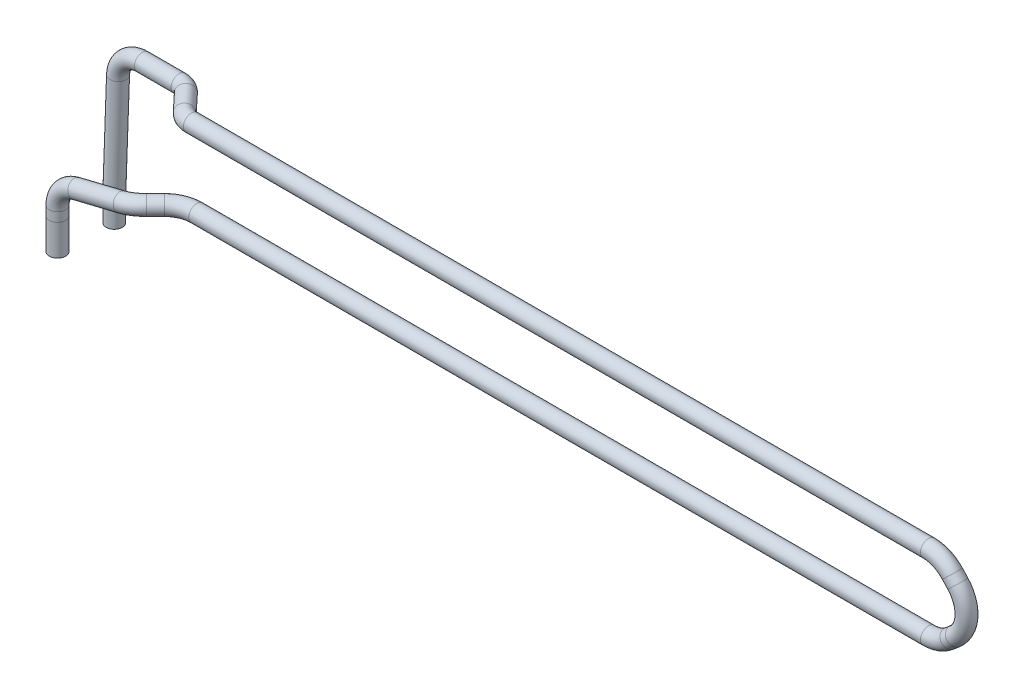
SolidWorks part; units mm, degrees
ref_plane "Front Plane" through (0, 0, 0) normal (0, 0, 1) x (1, 0, 0)
ref_plane "Top Plane" through (0, 0, 0) normal (0, 1, 0) x (1, 0, 0)
ref_plane "Right Plane" through (0, 0, 0) normal (1, 0, 0) x (0, 0, -1)
sketch3d "3DSketch1"
  line L0 (-61.7174, -11.5646, -3.1615) -> (-61.7174, -11.5646, 6.5143) construction
  line L1 (-62.0906, -9.4554, 3.4467) -> (-62.0906, -10.5909, 3.4467)
  line L3 (-52.0259, -4.8693, 2.533) -> (-50.944, -4.8693, 1.4511)
  line L4 (-48.1156, -4.8693, 0.2796) -> (41.8919, -4.8693, 0.2796)
  line L5 (44.494, -3.9073, 0.2796) -> (45.1703, -3.328, 0.2796)
  line L6 (45.4991, 2.432, 0.2796) -> (44.8228, 3.1602, 0.2796)
  line L7 (41.8919, 4.4381, 0.2796) -> (-48.7759, 4.4381, 0.2796)
  line L8 (-50.2366, 4.4381, -0.3542) -> (-52.2696, 4.4381, -2.5277)
  line L9 (-53.7302, 4.4381, -3.1615) -> (-58.2522, 4.4381, -3.1615)
  line L10 (-61.2503, 1.5449, -3.1615) -> (-61.7174, -11.5646, -3.1615)
  line L11 (-54.1951, -5.1752, 3.4467) -> (-59.8006, -6.5406, 3.4467)
  line L12 (-62.0906, -10.5909, 3.4467) -> (-62.0906, -14.4017, 3.4467)
  line L13 (-61.7174, -11.5646, -3.1615) -> (-61.7174, -14.4495, -3.1615)
  line L14 (41.8919, 4.4381, 0.2796) -> (41.8919, -4.8693, 0.2796) construction
  arc A0 (-61.2503, 1.5449, -3.1615) -> (-58.2522, 4.4381, -3.1615) centre (-58.2522, 1.4381, -3.1615) ccw
  arc A1 (-48.7759, 4.4381, 0.2796) -> (-50.2366, 4.4381, -0.3542) centre (-48.7759, 4.4381, -1.7204) ccw
  arc A2 (-53.7302, 4.4381, -3.1615) -> (-52.2696, 4.4381, -2.5277) centre (-53.7302, 4.4381, -1.1615) ccw
  arc A3 (-52.0259, -4.8693, 2.533) -> (-54.1951, -5.1752, 3.4467) centre (-54.0316, -5.8464, 0.5274) ccw
  arc A4 (-62.0906, -9.4554, 3.4467) -> (-59.8006, -6.5406, 3.4467) centre (-59.0906, -9.4554, 3.4467) ccw
  arc A5 (41.8919, 4.4381, 0.2796) -> (44.8228, 3.1602, 0.2796) centre (41.8919, 0.4381, 0.2796) ccw
  arc A6 (45.1703, -3.328, 0.2796) -> (45.4991, 2.432, 0.2796) centre (42.5682, -0.2901, 0.2796) ccw
  arc A7 (41.8919, -4.8693, 0.2796) -> (44.494, -3.9073, 0.2796) centre (41.8919, -0.8693, 0.2796) ccw
  arc A8 (-50.944, -4.8693, 1.4511) -> (-48.1156, -4.8693, 0.2796) centre (-48.1156, -4.8693, 4.2796) ccw
  point P16 (-61.1473, 4.4381, -3.1615)
  point P17 (-58.2522, 1.4381, -6.1615)
  point P20 (-49.6438, 4.4381, 0.2796)
  point P21 (-48.7759, 2.4381, -1.7204)
  point P24 (-52.8624, 4.4381, -3.1615)
  point P25 (-53.7302, 2.4381, -1.1615)
  point P27 (-52.9396, -4.8693, 3.4467)
  point P28 (-53.3406, -8.6829, 1.2183)
  point P31 (-62.0906, -7.0984, 3.4467)
  point P33 (-59.0906, -9.4554, 0.4467)
  point P36 (43.636, 4.4381, 0.2796)
  point P37 (41.8919, 0.4381, -3.7204)
  point P40 (48.3329, -0.6192, 0.2796)
  point P41 (42.5682, -0.2901, 4.2796)
  point P44 (43.3708, -4.8693, 0.2796)
  point P45 (41.8919, -0.8693, 4.2796)
  point P48 (-49.7725, -4.8693, 0.2796)
  point P49 (-48.1156, -8.8693, 4.2796)
  dimension "D1" = 3
  dimension "D2" = 2
  dimension "D3" = 3
  dimension "D4" = 4
  dimension "D5" = 4
  dimension "D6" = 93.2797
  dimension "D7" = 93.1433
ref_plane "Plane1" through (-61.7174, -11.5646, -3.1615) normal (-0.0356, -0.9994, 0) x (-0.9994, 0.0356, 0)
sketch "Sketch1" plane through (-61.7174, -11.5646, -3.1615) normal (-0.0356, -0.9994, 0) x (-0.9994, 0.0356, 0)
  circle A0 centre (0, 0) radius 1
  dimension "D1" = 2
ref_plane "Plane2" through (-61.2503, 1.5449, -3.1615) normal (-0.0356, -0.9994, 0) x (-0.9994, 0.0356, 0)
sketch "Sketch3" plane through (-61.2503, 1.5449, -3.1615) normal (-0.0356, -0.9994, 0) x (0.9994, -0.0356, 0)
ref_plane "Plane3" through (-48.7759, 4.4381, 0.2796) normal (-1, 0, 0) x (0, 0, 1)
sweep "Sweep1" add path "3DSketch1" circular profile diameter 2 parameters "D3"=2
